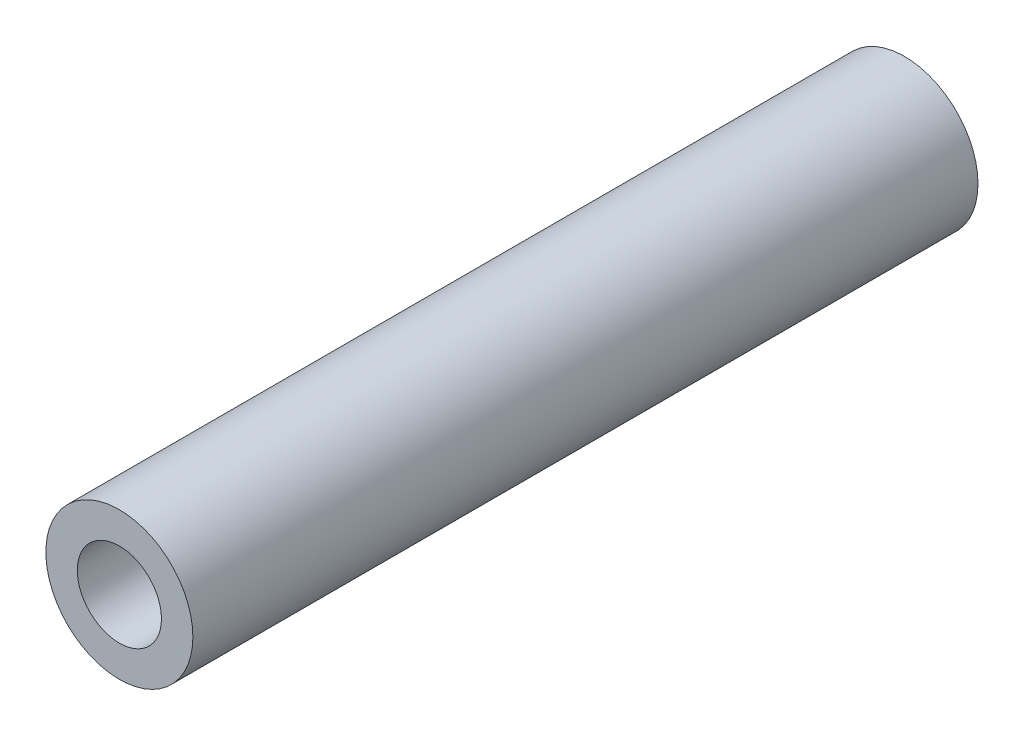
SolidWorks part; units mm, degrees
ref_plane "Front Plane" through (0, 0, 0) normal (0, 0, 1) x (1, 0, 0)
ref_plane "Top Plane" through (0, 0, 0) normal (0, 1, 0) x (1, 0, 0)
ref_plane "Right Plane" through (0, 0, 0) normal (1, 0, 0) x (0, 0, -1)
sketch "Sketch1" plane through (0, 0, 0) normal (0, 0, 1) x (1, 0, 0)
  circle A0 centre (1803.9912, -1743.8494) radius 4.63
  circle A1 centre (1803.9912, -1743.8494) radius 2.65
extrude "Boss-Extrude1" add sketch "Sketch1" along normal blind 49.45
